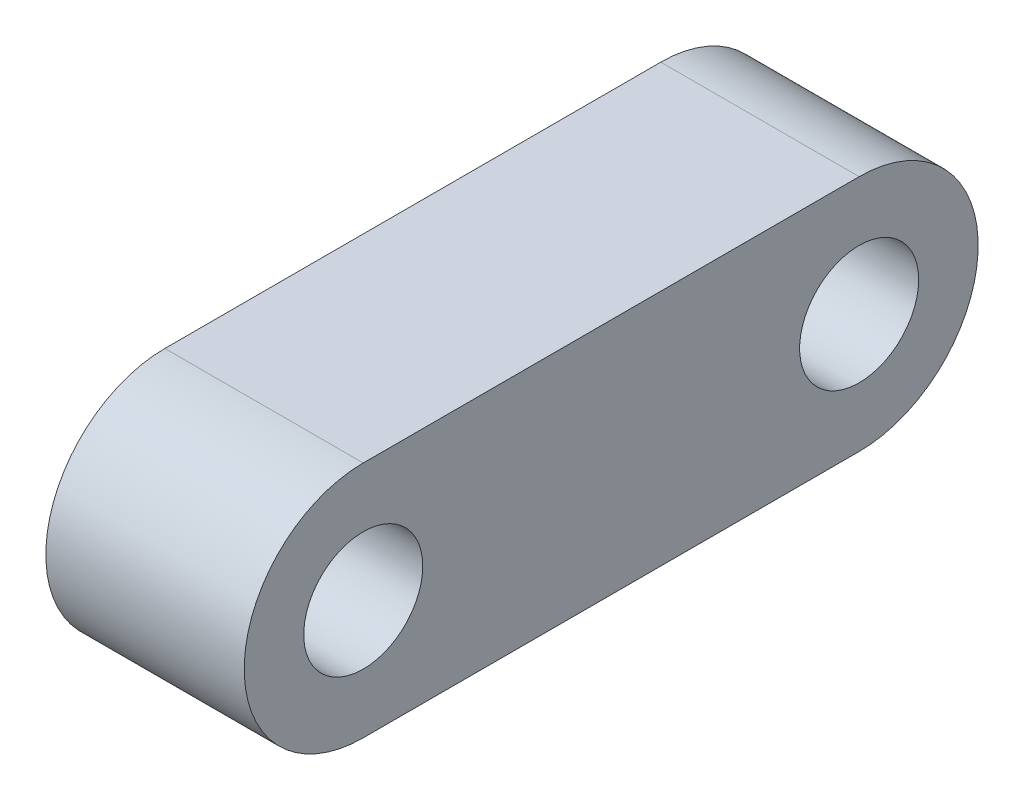
SolidWorks part; units mm, degrees
ref_plane "前视基准面" through (0, 0, 0) normal (0, 0, 1) x (1, 0, 0)
ref_plane "上视基准面" through (0, 0, 0) normal (0, 1, 0) x (1, 0, 0)
ref_plane "右视基准面" through (0, 0, 0) normal (1, 0, 0) x (0, 0, -1)
other "Configuration Table"
sketch "草图1" plane through (0, 0, 0) normal (1, 0, 0) x (0, 0, -1)
  line L0 (-6.25, 0) -> (6.25, 0) construction
  line L1 (-6.25, 0) -> (6.25, 0) construction
  line L2 (-6.25, 3) -> (6.25, 3)
  line L3 (-6.25, -3) -> (6.25, -3)
  circle A0 centre (6.25, 0) radius 1.5
  circle A1 centre (-6.25, 0) radius 1.5
  arc A2 (-6.25, 3) -> (-6.25, -3) centre (-6.25, 0) ccw
  arc A3 (6.25, -3) -> (6.25, 3) centre (6.25, 0) ccw
  point P4 (0, 0)
  point P8 (0, 0)
  dimension "D1" = 3
  dimension "D3" = 3
  dimension "D2" = 12.5
extrude "凸台-拉伸1" add sketch "草图1" along normal mid plane 5
